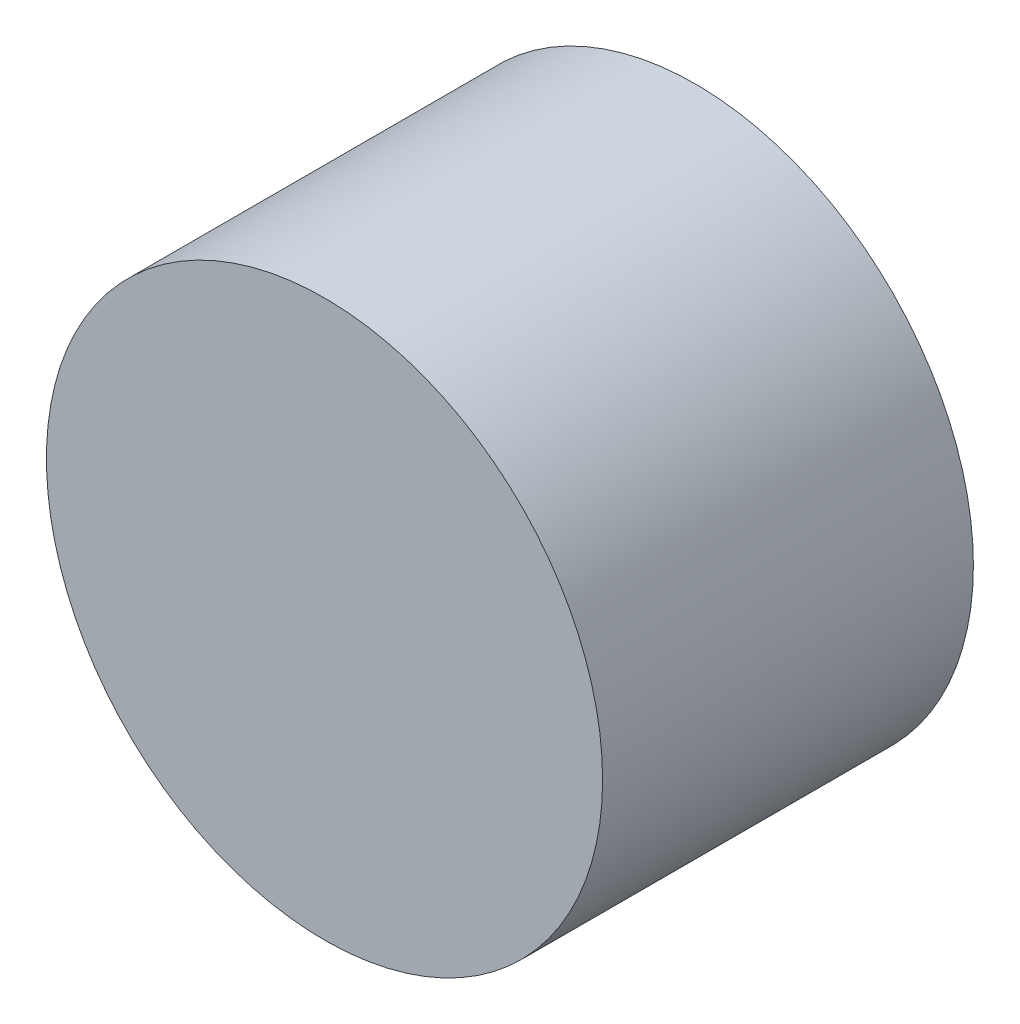
SolidWorks part; units mm, degrees
ref_plane "Alzado" through (0, 0, 0) normal (0, 0, 1) x (1, 0, 0)
ref_plane "Planta" through (0, 0, 0) normal (0, 1, 0) x (1, 0, 0)
ref_plane "Vista lateral" through (0, 0, 0) normal (1, 0, 0) x (0, 0, -1)
sketch "Sketch1" plane through (0, 0, 0) normal (0, 0, 1) x (1, 0, 0)
  circle A0 centre (0, 0.7482) radius 7.5
  dimension "D1" = 15
extrude "Boss-Extrude1" add sketch "Sketch1" along normal blind 10
